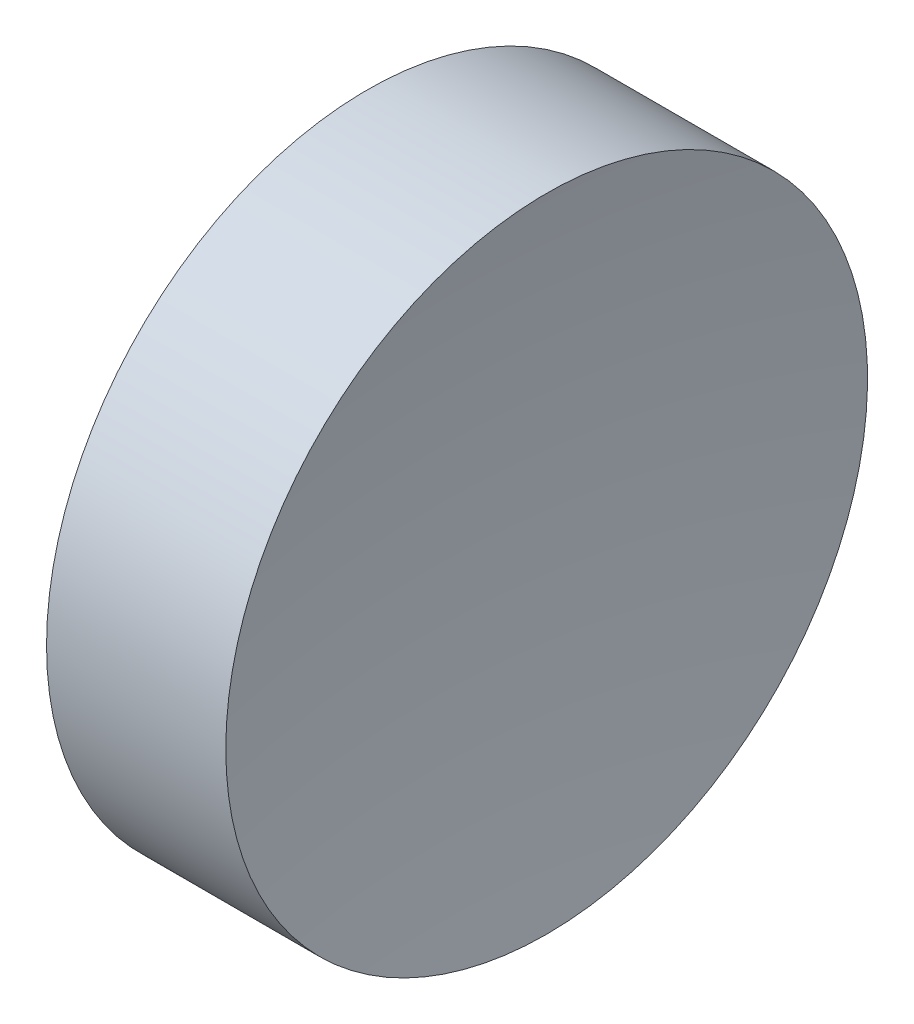
SolidWorks part; units mm, degrees
ref_plane "前视基准面" through (0, 0, 0) normal (0, 0, 1) x (1, 0, 0)
ref_plane "上视基准面" through (0, 0, 0) normal (0, 1, 0) x (1, 0, 0)
ref_plane "右视基准面" through (0, 0, 0) normal (1, 0, 0) x (0, 0, -1)
sketch "草图1" plane through (0, 0, 0) normal (0, 0, 1) x (1, 0, 0)
  line L0 (108.9851, 69.378) -> (132.7763, 69.378) construction
  line L1 (115.0927, 69.378) -> (115.0927, 81.878)
  line L2 (115.0927, 81.878) -> (122.0753, 81.878)
  line L3 (121.0927, 69.378) -> (115.0927, 69.378)
  arc A0 (122.0753, 81.878) -> (121.0927, 69.378) centre (201.0927, 69.378) ccw
revolve "旋转1" add sketch "草图1" angle 360 about L0
